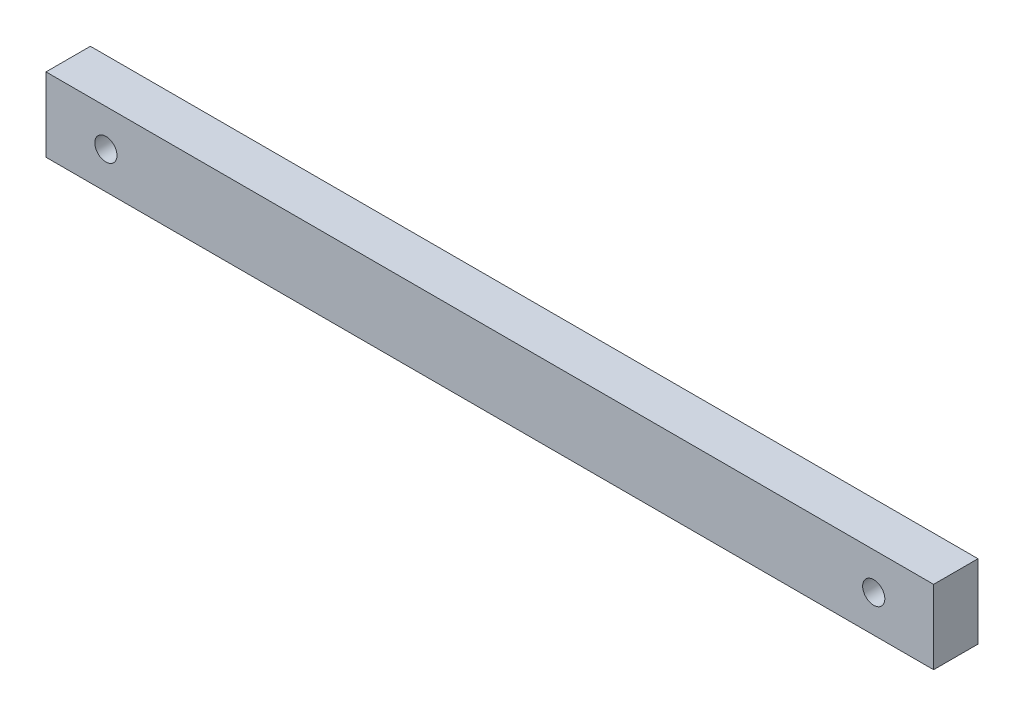
SolidWorks part; units mm, degrees
ref_plane "前视基准面" through (0, 0, 0) normal (0, 0, 1) x (1, 0, 0)
ref_plane "上视基准面" through (0, 0, 0) normal (0, 1, 0) x (1, 0, 0)
ref_plane "右视基准面" through (0, 0, 0) normal (1, 0, 0) x (0, 0, -1)
sketch "草图1" plane through (0, 0, 0) normal (0, 0, 1) x (1, 0, 0)
  line L1 (-64.2084, 20.3206) -> (55.7916, 20.3206)
  line L2 (-64.2084, 20.3206) -> (-64.2084, 10.3206)
  line L3 (-64.2084, 10.3206) -> (55.7916, 10.3206)
  line L4 (55.7916, 20.3206) -> (55.7916, 10.3206)
  dimension "D1" = 120
  dimension "D2" = 10
extrude "凸台-拉伸1" add sketch "草图1" along normal blind 6
sketch "草图2" plane through (0, 0, 6) normal (0, 0, 1) x (1, 0, 0)
  line L0 (-64.2084, 15.3206) -> (55.7916, 15.3206)
  line L1 (-64.2084, 20.3206) -> (-64.2084, 10.3206) construction
  line L2 (55.7916, 10.3206) -> (55.7916, 20.3206) construction
  line L3 (-4.2084, 20.3206) -> (-4.2084, 10.3206)
  line L4 (55.7916, 20.3206) -> (-64.2084, 20.3206) construction
  line L5 (-64.2084, 10.3206) -> (55.7916, 10.3206) construction
  circle A0 centre (-56.1126, 15.3206) radius 1.5
  circle A1 centre (47.6958, 15.3206) radius 1.5
extrude "切除-拉伸1" cut sketch "草图2" against normal through all contours A0 | A1
